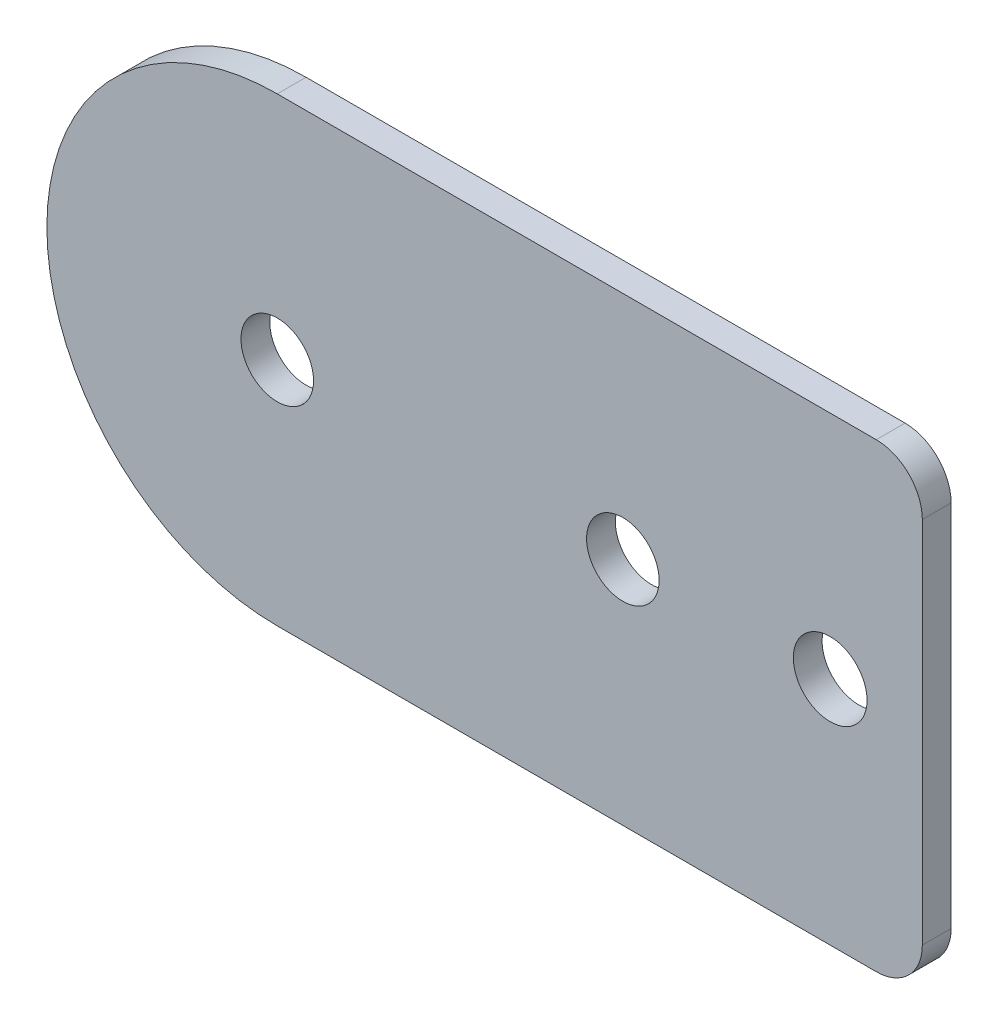
SolidWorks part; units mm, degrees
ref_plane "Front Plane" through (0, 0, 0) normal (0, 0, 1) x (1, 0, 0)
ref_plane "Top Plane" through (0, 0, 0) normal (0, 1, 0) x (1, 0, 0)
ref_plane "Right Plane" through (0, 0, 0) normal (1, 0, 0) x (0, 0, -1)
sketch "Sketch1" plane through (0, 0, 0) normal (0, 0, 1) x (1, 0, 0)
  line L0 (0, 0) -> (19.05, 0) construction
  line L1 (0, -12.7) -> (35.56, -12.7)
  line L2 (0, -12.7) -> (0, 12.7) construction
  line L3 (0, 12.7) -> (35.56, 12.7)
  line L4 (35.56, -12.7) -> (35.56, 12.7)
  line L5 (19.05, 0) -> (30.48, 0) construction
  arc A0 (0, 12.7) -> (0, -12.7) centre (0, 0) ccw
  circle A1 centre (0, 0) radius 2
  circle A2 centre (19.05, 0) radius 2
  circle A3 centre (30.48, 0) radius 2.032
  dimension "D3" = 4
  dimension "D4" = 4
  dimension "D6" = 4.064
  dimension "D1" = 25.4
  dimension "D2" = 35.56
  dimension "D5" = 19.05
  dimension "D7" = 11.43
extrude "Boss-Extrude1" add sketch "Sketch1" along normal blind 1.5875
fillet "Fillet1" radius 2.54 2 edges at (35.56, -12.7, 0.7937) (35.56, 12.7, 0.7937)
